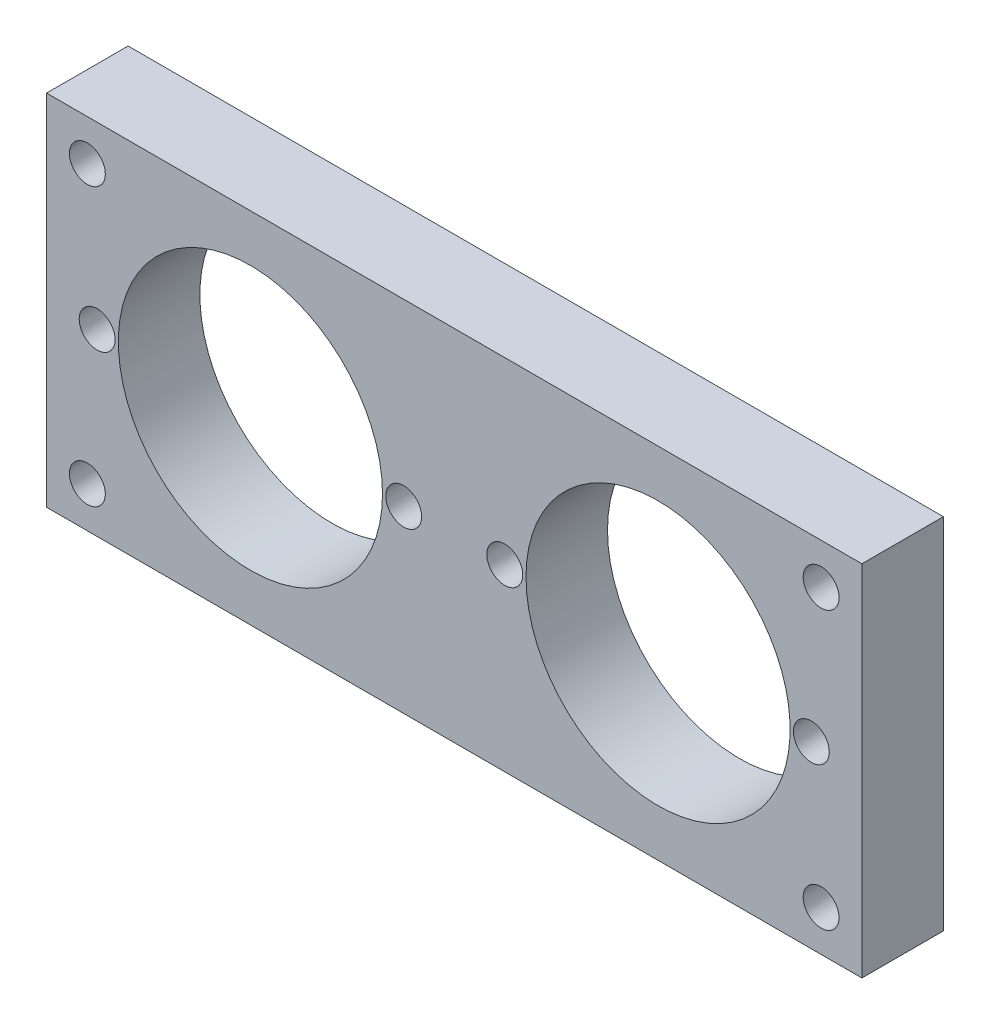
SolidWorks part; units mm, degrees
ref_plane "前视基准面" through (0, 0, 0) normal (0, 0, 1) x (1, 0, 0)
ref_plane "上视基准面" through (0, 0, 0) normal (0, 1, 0) x (1, 0, 0)
ref_plane "右视基准面" through (0, 0, 0) normal (1, 0, 0) x (0, 0, -1)
sketch "草图1" plane through (0, 0, 0) normal (0, 0, 1) x (1, 0, 0)
  line L0 (12.5, 0) -> (12.5, -8.1) construction
  line L1 (-25, 11) -> (25, 11)
  line L2 (-25, 11) -> (-25, -11)
  line L3 (-25, -11) -> (25, -11)
  line L4 (25, 11) -> (25, -11)
  line L5 (0, -11) -> (0, 11) construction
  line L6 (-25, 0) -> (25, 0) construction
  circle A0 centre (-22.5, 8.5) radius 1.1
  circle A1 centre (22.5, 8.5) radius 1.1
  circle A2 centre (22.5, -8.5) radius 1.1
  circle A3 centre (-22.5, -8.5) radius 1.1
  circle A4 centre (-12.5, 0) radius 8.1
  circle A5 centre (12.5, 0) radius 8.1
  circle A6 centre (21.9, 0) radius 1.1
  circle A7 centre (-21.9, 0) radius 1.1
  circle A8 centre (3.1, 0) radius 1.1
  circle A9 centre (-3.1, 0) radius 1.1
  point P0 (0, 0)
  dimension "D3" = 2.2
  dimension "D4" = 45
  dimension "D5" = 17
  dimension "D6" = 16.2
  dimension "D8" = 2.2
  dimension "D1" = 22
  dimension "D2" = 50
  dimension "D7" = 25
  dimension "D9" = 3.1
extrude "凸台-拉伸1" add sketch "草图1" along normal blind 5
